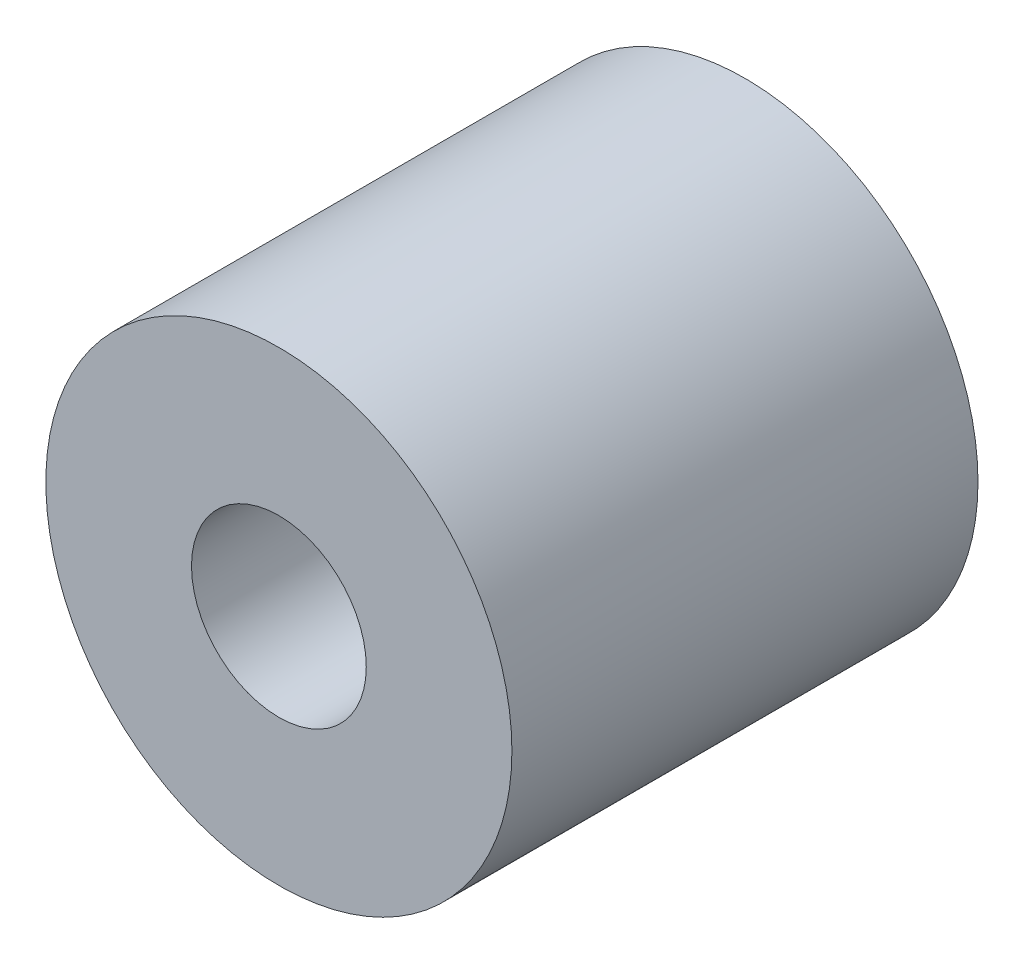
SolidWorks part; units mm, degrees
ref_plane "Piano frontale" through (0, 0, 0) normal (0, 0, 1) x (1, 0, 0)
ref_plane "Piano superiore" through (0, 0, 0) normal (0, 1, 0) x (1, 0, 0)
ref_plane "Piano destro" through (0, 0, 0) normal (1, 0, 0) x (0, 0, -1)
sketch "Schizzo1" plane through (0, 0, 0) normal (0, 0, 1) x (1, 0, 0)
  circle A0 centre (0, 0) radius 1.5
  circle A1 centre (0, 0) radius 4
  dimension "D1" = 3
  dimension "D2" = 8
extrude "Estrusione-Estrusione1" add sketch "Schizzo1" along normal blind 8
